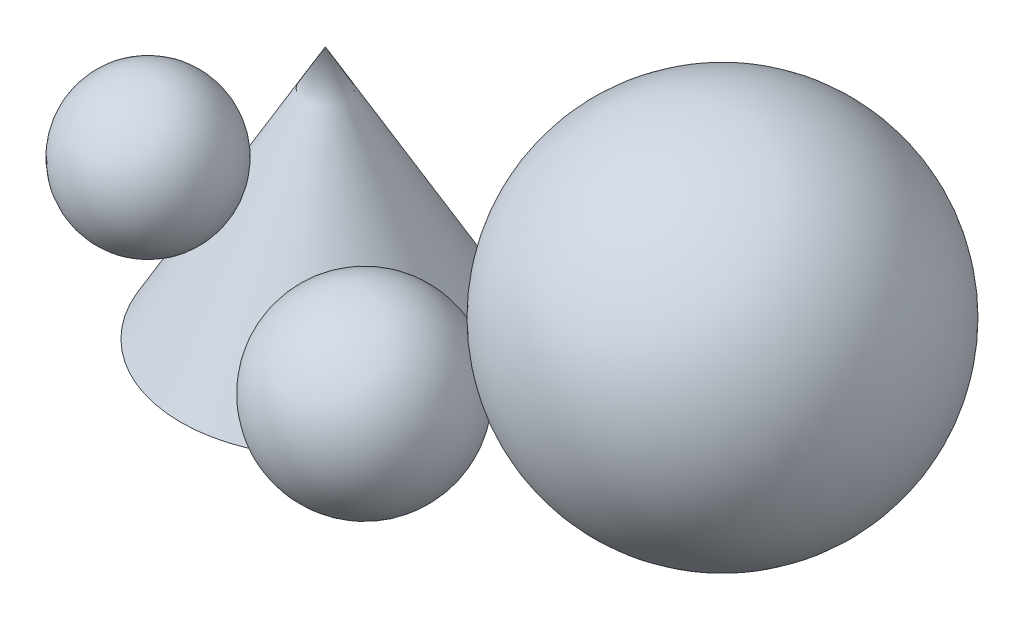
SolidWorks part; units mm, degrees
ref_plane "Front Plane" through (0, 0, 0) normal (0, 0, 1) x (1, 0, 0)
ref_plane "Top Plane" through (0, 0, 0) normal (0, 1, 0) x (1, 0, 0)
ref_plane "Right Plane" through (0, 0, 0) normal (1, 0, 0) x (0, 0, -1)
sketch "Sketch1" plane through (0, 0, 0) normal (0, 0, 1) x (1, 0, 0)
  line L0 (0, 0) -> (-40, 70)
  line L1 (-40, 70) -> (-40, 0)
  line L2 (-40, 0) -> (0, 0)
  dimension "D1" = 40
  dimension "D2" = 70
revolve "Revolve1" add sketch "Sketch1" angle 360 about L1
sketch "Sketch2" plane through (0, 0, 0) normal (0, 1, 0) x (1, 0, 0)
  line L0 (-40, 0) -> (-40, 63.8569) construction
  line L1 (-40, -40) -> (83.7103, -40) construction
  circle A0 centre (60, 10) radius 50 construction
  circle A1 centre (-40, 0) radius 40 construction
  dimension "D1" = 100
  dimension "D2" = 100
ref_plane "Plane1" through (0, 0, -10) normal (0, 0, 1) x (1, 0, 0)
sketch "Sketch3" plane through (0, 0, -10) normal (0, 0, 1) x (1, 0, 0)
  line L0 (59.7727, 99.9999) -> (60, 0)
  line L1 (110, 0) -> (10, 0) construction
  arc A0 (60, 0.0001) -> (59.7727, 99.9999) centre (59.8863, 50) ccw
  dimension "D1" = 100
  dimension "D2" = 50
revolve "Revolve2" add sketch "Sketch3" angle 360 about L0
sketch "Sketch4" plane through (0, 0, 0) normal (0, 0, 1) x (1, 0, 0)
  line L0 (-80, 0) -> (-103.1849, 0) construction
  line L1 (-40, 70) -> (-80, 0) construction
  circle A0 centre (-94.5081, 25) radius 25 construction
  dimension "D1" = 50
sketch "Sketch5" plane through (0, 0, -10) normal (0, 0, 1) x (1, 0, 0)
  line L0 (59.8863, 0) -> (158.4324, 0) construction
  circle A0 centre (59.8863, 50) radius 50 construction
  circle A1 centre (130.597, 25) radius 25 construction
  dimension "D1" = 50
ref_plane "Plane2" through (0, 25, 0) normal (0, 1, 0) x (-1, 0, 0)
sketch "Sketch6" plane through (0, 25, 0) normal (0, 1, 0) x (-1, 0, 0)
  line L0 (-59.8863, 40) -> (-59.8863, -60) construction
  line L1 (40, 40) -> (40, -40) construction
  line L2 (-3.5673, 57.757) -> (-3.5673, 7.757)
  circle A0 centre (-59.8863, -10) radius 50 construction
  circle A1 centre (40, 0) radius 40 construction
  circle A2 centre (40, 0) radius 54.5081 construction
  circle A3 centre (-59.8863, -10) radius 70.7107 construction
  arc A4 (-3.5673, 7.757) -> (-3.5673, 57.757) centre (-3.5673, 32.757) ccw
  dimension "D1" = 50
revolve "Revolve3" add sketch "Sketch6" angle 360 about L2
sketch "Sketch7" plane through (0, 0, 0) normal (0, 1, 0) x (1, 0, 0)
  line L0 (-40, 40) -> (-40, -40) construction
  line L1 (-80, 0) -> (-40, 0) construction
  line L2 (-80, -15) -> (-40, -15) construction
  line L3 (-50, 40) -> (-50, -40) construction
  line L4 (-40, 0) -> (-50, -15)
  circle A0 centre (-40, 0) radius 40 construction
  dimension "D1" = 15
  dimension "D2" = 10
ref_plane "Plane3" through (-27.6923, 0, -18.4615) normal (-0.8321, 0, -0.5547) x (-0.5547, 0, 0.8321)
sketch "Sketch8" plane through (-27.6923, 0, -18.4615) normal (-0.8321, 0, -0.5547) x (-0.5547, 0, 0.8321)
  line L0 (22.188, 70) -> (22.188, 0) construction
  line L1 (40.2158, 0) -> (40.2158, 63.1282) construction
  line L2 (22.188, 70) -> (62.188, 0) construction
  line L3 (40.2158, 38.4514) -> (57.5806, 48.3742) construction
  line L4 (57.5806, 68.3742) -> (57.5806, 28.3742)
  arc A0 (57.5806, 68.3742) -> (57.5806, 28.3742) centre (57.5806, 48.3742) ccw
  dimension "D1" = 40
revolve "Revolve4" add sketch "Sketch8" angle 360 about L4
